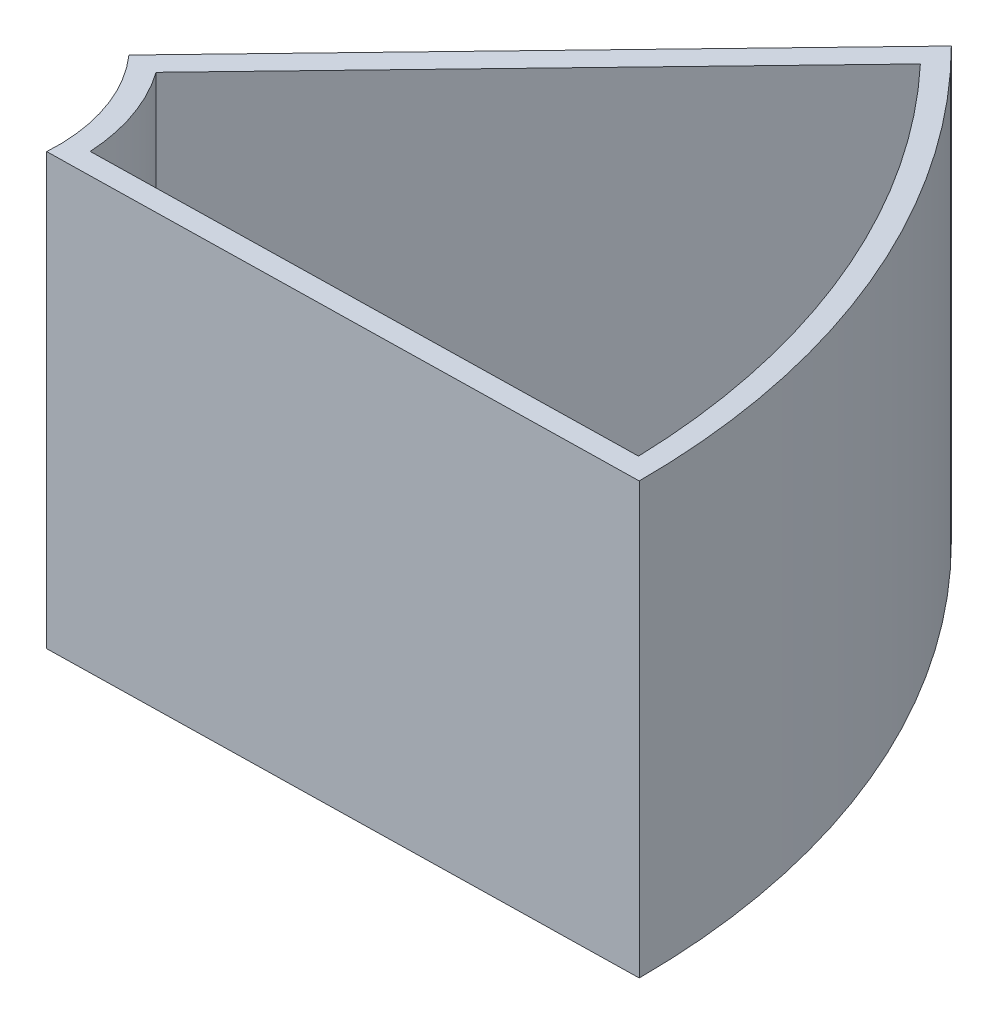
SolidWorks part; units mm, degrees
ref_plane "Front Plane" through (0, 0, 0) normal (0, 0, 1) x (1, 0, 0)
ref_plane "Top Plane" through (0, 0, 0) normal (0, 1, 0) x (1, 0, 0)
ref_plane "Right Plane" through (0, 0, 0) normal (1, 0, 0) x (0, 0, -1)
sketch "Sketch3" plane through (0, 0, 0) normal (0, 1, 0) x (1, 0, 0)
  line L0 (123.7437, 123.7437) -> (30.0457, 26.4056)
  line L1 (175, 0) -> (39.9171, -2.5739)
  line L2 (36.6721, 26.0798) -> (123.7587, 116.5495)
  line L3 (169.9292, 4.9043) -> (44.9292, 2.5225)
  arc A0 (175, 0) -> (123.7437, 123.7437) centre (0, 0) ccw
  arc A1 (39.9171, -2.5739) -> (30.0457, 26.4056) centre (0, 0) ccw
  arc A2 (36.6721, 26.0798) -> (44.9292, 2.5225) centre (0, 0) cw
  arc A3 (123.7587, 116.5495) -> (169.9292, 4.9043) centre (0, 0) cw
  dimension "D7" = 170
  dimension "D9" = 5
  dimension "D8" = 125
  dimension "D1" = 175
  dimension "D2" = 45
  dimension "D3" = 5
  dimension "D4" = 40
  dimension "D5" = 45
  dimension "D10" = 5
  dimension "D12" = 5
  dimension "D13" = 5
extrude "Boss-Extrude1" add sketch "Sketch3" along normal blind 100
sketch "Sketch5" plane through (0, 0, 0) normal (0, 1, 0) x (1, 0, 0)
  line L0 (123.7437, 123.7437) -> (30.0457, 26.4056)
  line L2 (39.9171, -2.5739) -> (175, 0)
  arc A0 (30.0457, 26.4056) -> (39.9171, -2.5739) centre (0, 0) cw
  arc A1 (175, 0) -> (123.7437, 123.7437) centre (0, 0) ccw
extrude "Boss-Extrude3" add sketch "Sketch5" along normal blind 15 contours L2 A1 L0 A0
